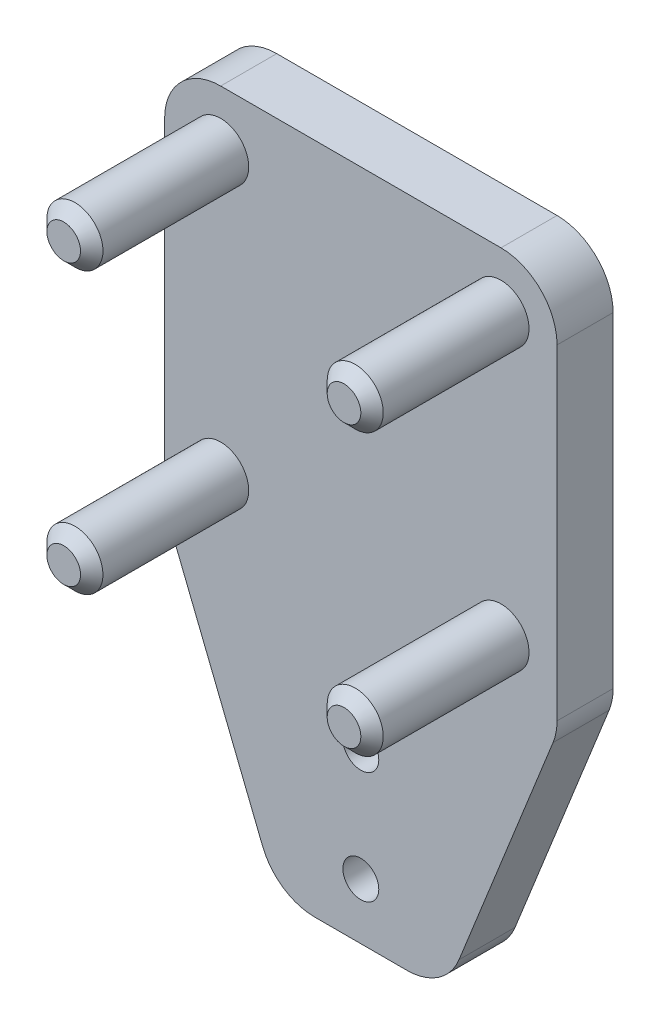
SolidWorks part; units mm, degrees
ref_plane "Front Plane" through (0, 0, 0) normal (0, 0, 1) x (1, 0, 0)
ref_plane "Top Plane" through (0, 0, 0) normal (0, 1, 0) x (1, 0, 0)
ref_plane "Right Plane" through (0, 0, 0) normal (1, 0, 0) x (0, 0, -1)
sketch "Sketch1" plane through (0, 0, 0) normal (0, 0, 1) x (1, 0, 0)
  line L1 (0, 0) -> (35, 0)
  line L2 (0, 0) -> (0, -35)
  line L3 (0, -35) -> (35, -35)
  line L4 (35, 0) -> (35, -35)
  dimension "D1" = 35
extrude "Boss-Extrude1" add sketch "Sketch1" along normal blind 5 contours L4 L3 L2 L1
sketch "Sketch2" plane through (0, 0, 5) normal (0, 0, 1) x (1, 0, 0)
  line L0 (0, 0) -> (0, -35) construction
  line L2 (0, 0) -> (35, 0) construction
  line L3 (17.5, 0) -> (17.5, -7.0215) construction
  line L4 (35, -17.5) -> (28.4428, -17.5) construction
  line L5 (35, 0) -> (35, -35) construction
  line L6 (0, -17.5) -> (6.5572, -17.5) construction
  circle A0 centre (5, -5) radius 2.5
  circle A1 centre (30, -5) radius 2.5
  circle A2 centre (30, -30) radius 2.5
  circle A3 centre (5, -30) radius 2.5
  dimension "D1" = 5
  dimension "D2" = 5
  dimension "D3" = 5
extrude "Boss-Extrude2" add sketch "Sketch2" along normal blind 14
fillet "Fillet1" radius 5 4 edges at (0, 0, 2.5) (0, -35, 2.5) (35, -35, 2.5) (35, 0, 2.5)
chamfer "Chamfer1" distance 1 angle 45 4 edges at (32.5, -30, 19) (27.5, -5, 19) (2.5, -30, 19) (7.5, -5, 19)
sketch "Sketch3" plane through (0, 0, 0) normal (0, 0, -1) x (-1, 0, 0)
  line L0 (-35, -30) -> (-35, -35)
  line L1 (0, -30) -> (0, -35)
  line L2 (0, -35) -> (-10, -60)
  line L3 (-25, -60) -> (-35, -35)
  line L4 (-5, -35) -> (-30, -35) construction
  line L5 (-27.9423, -35) -> (-5, -35)
  line L7 (-25, -60) -> (-10, -60)
  line L9 (-35, -30) -> (0, -30)
  point P8 (0, 0)
  dimension "D1" = 15
  dimension "D2" = 10
extrude "Boss-Extrude3" add sketch "Sketch3" against normal up to surface (5 mm away) contours L2 L7 L3 L0 L9 L1 up to face at (2.5, -30, 5)
sketch "Sketch5" plane through (0, 0, 5) normal (0, 0, 1) x (1, 0, 0)
  line L0 (10, -60) -> (25, -60) construction
  circle A0 centre (17.5, -55) radius 1.6
  circle A1 centre (17.5, -45) radius 1.6
  dimension "D1" = 3.2
  dimension "D2" = 3.2
  dimension "D3" = 10
  dimension "D4" = 5
extrude "Cut-Extrude1" cut sketch "Sketch5" against normal blind 14 contours A1 | A0
fillet "Fillet2" radius 5 4 edges at (35, -35, 2.5) (0, -35, 2.5) (25, -60, 2.5) (10, -60, 2.5)
